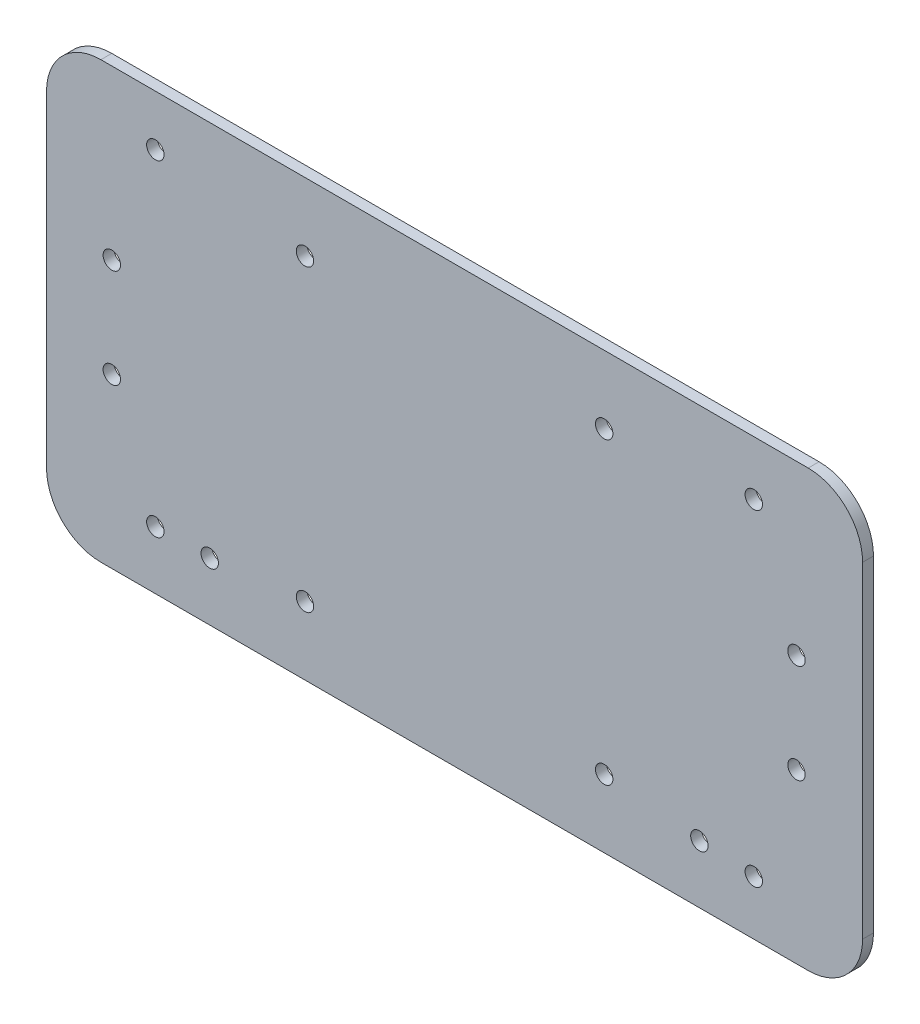
SolidWorks part; units mm, degrees
ref_plane "Front Plane" through (0, 0, 0) normal (0, 0, 1) x (1, 0, 0)
ref_plane "Top Plane" through (0, 0, 0) normal (0, 1, 0) x (1, 0, 0)
ref_plane "Right Plane" through (0, 0, 0) normal (1, 0, 0) x (0, 0, -1)
sketch "Sketch1" plane through (0, 0, 0) normal (0, 0, 1) x (1, 0, 0)
  line L0 (-75, 0) -> (-63, 0) construction
  line L1 (-65, -40) -> (65, -40)
  line L2 (-75, -30) -> (-75, 30)
  line L3 (-65, 40) -> (65, 40)
  line L4 (75, -30) -> (75, 30)
  line L5 (75, 0) -> (62.85, 0) construction
  line L6 (-63, 0) -> (-63, 9.1) construction
  line L7 (-63, 0) -> (-63, -9.1) construction
  line L8 (62.85, 0) -> (62.85, -9.1) construction
  line L9 (62.85, 0) -> (62.85, 9.1) construction
  line L10 (-75, 40) -> (75, -40) construction
  line L11 (-75, -40) -> (75, 40) construction
  line L12 (75, 40) -> (75, 30) construction
  line L13 (40, 40) -> (-40, 40)
  line L14 (40, 40) -> (40, -40)
  line L15 (40, -40) -> (-40, -40)
  line L16 (-40, 40) -> (-40, -40)
  line L17 (0, -40) -> (0, 40) construction
  line L18 (40, 0) -> (-40, 0) construction
  line L19 (75, 30) -> (55, 30) construction
  line L20 (55, 30) -> (55, -30) construction
  line L21 (-75, 40) -> (-75, 30.6667) construction
  line L22 (-75, 30.6667) -> (-55, 30.6667) construction
  line L23 (-55, 30.6667) -> (-55, -29.3333) construction
  line L24 (-40, -40) -> (-40, -27.5) construction
  line L25 (-40, -27.5) -> (-27.5, -27.5) construction
  line L26 (-27.5, -27.5) -> (27.5, -27.5) construction
  line L27 (-27.5, -27.5) -> (-27.5, 27.5) construction
  line L28 (-27.5, 27.5) -> (27.5, 27.5) construction
  circle A0 centre (-63, 9.1) radius 1.6
  circle A1 centre (-63, -9.1) radius 1.6
  circle A2 centre (62.85, 9.1) radius 1.6
  circle A3 centre (62.85, -9.1) radius 1.6
  circle A4 centre (55, 30) radius 1.6
  circle A5 centre (55, -30) radius 1.6
  circle A6 centre (-55, -29.3333) radius 1.6
  circle A7 centre (-55, 30.6667) radius 1.6
  circle A8 centre (-45, -29.3333) radius 1.6
  circle A9 centre (45, -29.3333) radius 1.6
  circle A10 centre (-27.5, -27.5) radius 1.6
  circle A11 centre (27.5, -27.5) radius 1.6
  circle A12 centre (-27.5, 27.5) radius 1.6
  circle A13 centre (27.5, 27.5) radius 1.6
  arc A14 (-75, 30) -> (-65, 40) centre (-65, 30) cw
  arc A15 (-75, -30) -> (-65, -40) centre (-65, -30) ccw
  arc A16 (65, -40) -> (75, -30) centre (65, -30) ccw
  arc A17 (75, 30) -> (65, 40) centre (65, 30) ccw
  point P0 (0, 0)
  point P16 (0, 0)
  point P34 (0, -29.3333)
  dimension "D3" = 12
  dimension "D6" = 18.2
  dimension "D7" = 110
  dimension "D9" = 90
  dimension "D10" = 10
  dimension "D11" = 10
  dimension "D12" = 10
  dimension "D13" = 10
  dimension "D1" = 150
  dimension "D2" = 80
  dimension "D4" = 12.15
  dimension "D5" = 10
  dimension "D8" = 60
extrude "Boss-Extrude1" add sketch "Sketch1" along normal blind 2 contours L3 L14 L1 L4 A5 A4 A3 A2 | L3 L16 L1 L14 | L16 L3 L2 L1 A7 A6 A1 A0
